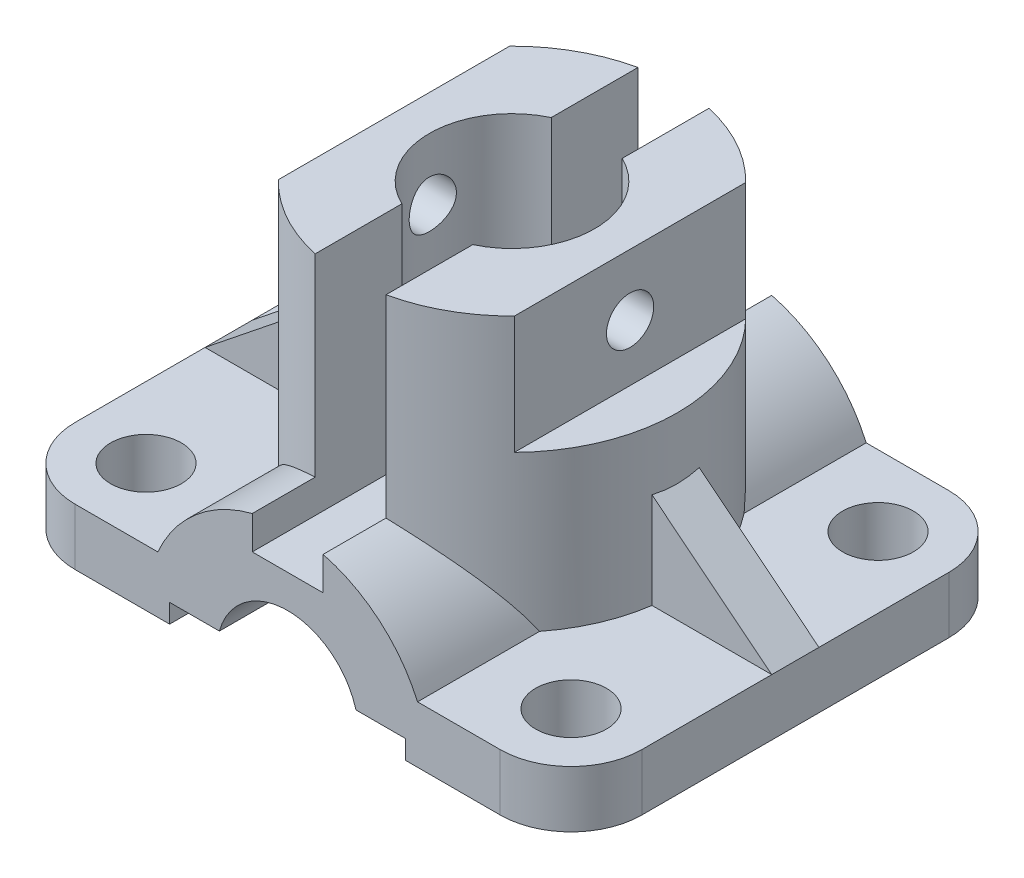
SolidWorks part; units mm, degrees
material "灰铸铁"
ref_plane "前视基准面" through (0, 0, 0) normal (0, 0, 1) x (1, 0, 0)
ref_plane "上视基准面" through (0, 0, 0) normal (0, 1, 0) x (1, 0, 0)
ref_plane "右视基准面" through (0, 0, 0) normal (1, 0, 0) x (0, 0, -1)
sketch "草图1" plane through (0, 0, 0) normal (0, 1, 0) x (1, 0, 0)
  line L1 (-45, 47.5) -> (45, 47.5)
  line L2 (-60, 32.5) -> (-60, -32.5)
  line L3 (-45, -47.5) -> (45, -47.5)
  line L4 (60, 32.5) -> (60, -32.5)
  line L5 (-60, 47.5) -> (60, -47.5) construction
  line L6 (-60, -47.5) -> (60, 47.5) construction
  arc A0 (-60, -32.5) -> (-45, -47.5) centre (-45, -32.5) ccw
  arc A1 (45, -47.5) -> (60, -32.5) centre (45, -32.5) ccw
  arc A2 (45, 47.5) -> (60, 32.5) centre (45, 32.5) cw
  arc A3 (-45, 47.5) -> (-60, 32.5) centre (-45, 32.5) ccw
  point P0 (0, 0)
  dimension "D1" = 15
  dimension "D2" = 120
  dimension "D3" = 95
extrude "凸台-拉伸1" add sketch "草图1" along normal blind 12
sketch "草图2" plane through (0, 0, 47.5) normal (0, 0, 1) x (1, 0, 0)
  line L0 (-45, 0) -> (45, 0) construction
  line L1 (-30, 0) -> (30, 0)
  arc A0 (30, 0) -> (-30, 0) centre (0, 0) ccw
  dimension "D1" = 30
extrude "凸台-拉伸2" add sketch "草图2" against normal through all
sketch "草图3" plane through (0, 0, 0) normal (0, 0, 1) x (1, 0, 0)
  line L0 (0, 0) -> (0, 58.1031) construction
  line L2 (0, 0) -> (35, 0)
  line L3 (0, 0) -> (0, 70)
  line L4 (0, 70) -> (35, 70)
  line L5 (35, 0) -> (35, 70)
  dimension "D1" = 70
  dimension "D2" = 70
revolve "旋转1" add sketch "草图3" angle 360 about L0
sketch "草图4" plane through (0, 0, 0) normal (0, 0, 1) x (1, 0, 0)
  line L0 (-60, 12) -> (-35, 32)
  line L1 (-35, 70) -> (-35, 12) construction
  dimension "D1" = 20
rib "筋1" sketch "草图4" sketch "草图4" thickness 10 extrusion direction parallel to sketch draft on no parameters "D1"=10
mirror "镜向1" about plane through (0, 0, 0) normal (1, 0, 0) of "筋1"
hole_wizard "Ø15.0 (15) 直径孔1" positions "草图6" profile "草图5" hole size "Ø15.0" standard "GB" end condition through all
sketch "草图6" plane through (0, 12, 0) normal (0, 1, 0) x (1, 0, 0)
  point P0 (-45, -32.5)
sketch "草图5" plane through (-45, 12, 32.5) normal (1, 0, 0) x (0, 0, 1)
  line L0 (0, 0) -> (0, 12)
  line L1 (0, 12) -> (7.5, 12)
  line L2 (7.5, 12) -> (7.5, 0)
  line L5 (7.5, 0) -> (0, 0)
  line L11 (0, -6.35) -> (0, 107.95) construction
  dimension "通孔孔直径" = 15
  dimension "通孔孔深度" = 12
pattern_linear "阵列(线性)2" count 2 spacing 90 along (1, 0, 0) count 2 spacing 65 along (0, 0, -1) of "Ø15.0 (15) 直径孔1"
sketch "草图7" plane through (0, 0, 47.5) normal (0, 0, 1) x (1, 0, 0)
  line L0 (0, 0) -> (0, 82.5766) construction
  line L1 (-45, 0) -> (45, 0) construction
  line L2 (-25, 0) -> (25, 0)
  line L3 (-25, 0) -> (-25, 4)
  line L4 (-25, 4) -> (-14.4568, 4)
  line L5 (25, 0) -> (25, 4)
  line L6 (14.4568, 4) -> (25, 4)
  arc A0 (14.4568, 4) -> (-14.4568, 4) centre (0, 0) ccw
  dimension "D2" = 15
  dimension "D1" = 50
  dimension "D3" = 4
extrude "切除-拉伸1" cut sketch "草图7" against normal through all
sketch "草图9" plane through (0, 70, 0) normal (0, 1, 0) x (1, 0, 0)
  circle A0 centre (0, 0) radius 17.5
  dimension "D1" = 35
extrude "切除-拉伸2" cut sketch "草图9" against normal through all
sketch "草图10" plane through (0, 70, 0) normal (0, 1, 0) x (1, 0, 0)
  line L0 (-25, 24.4949) -> (-25, -24.4949)
  line L1 (25, 24.4949) -> (25, -24.4949)
  arc A0 (25, -24.4949) -> (25, 24.4949) centre (0, 0) ccw
  circle A1 centre (0, 0) radius 35
  arc A2 (-25, 24.4949) -> (-25, -24.4949) centre (0, 0) ccw
  dimension "D2" = 50
  dimension "D1" = 0
extrude "切除-拉伸3" cut sketch "草图10" against normal blind 25
hole_wizard "Ø10.0 (10) 直径孔2" positions "草图14" profile "草图13" hole size "Ø10.0" standard "GB" end condition through all
sketch "草图14" plane through (-25, 0, 0) normal (-1, 0, 0) x (0, 0, 1)
  line L0 (0, -38.5) -> (0, 38.5) construction
  line L1 (24.4949, 70) -> (-24.4949, 70) construction
  point P0 (0, 57)
  point P5 (0, 70)
  dimension "D1" = 13
sketch "草图13" plane through (-25, 57, 0) normal (0, 1, 0) x (0, 0, 1)
  line L0 (0, 0) -> (0, 85)
  line L1 (0, 85) -> (5, 85)
  line L2 (5, 85) -> (5, 0)
  line L5 (5, 0) -> (0, 0)
  line L11 (0, -6.35) -> (0, 107.95) construction
  dimension "通孔孔直径" = 10
  dimension "通孔孔深度" = 85
sketch "草图22" plane through (0, 0, -47.5) normal (0, 0, -1) x (-1, 0, 0)
  line L0 (0, 0) -> (0, 77.4986) construction
  line L1 (25, 70) -> (-25, 70) construction
  line L2 (-7.5, 70) -> (7.5, 70)
  line L3 (-7.5, 70) -> (-7.5, 22)
  line L4 (-7.5, 22) -> (7.5, 22)
  line L5 (7.5, 70) -> (7.5, 22)
  dimension "D1" = 15
  dimension "D2" = 48
extrude "切除-拉伸6" cut sketch "草图22" against normal through all
fillet "圆角20" [suppressed] radius 2
